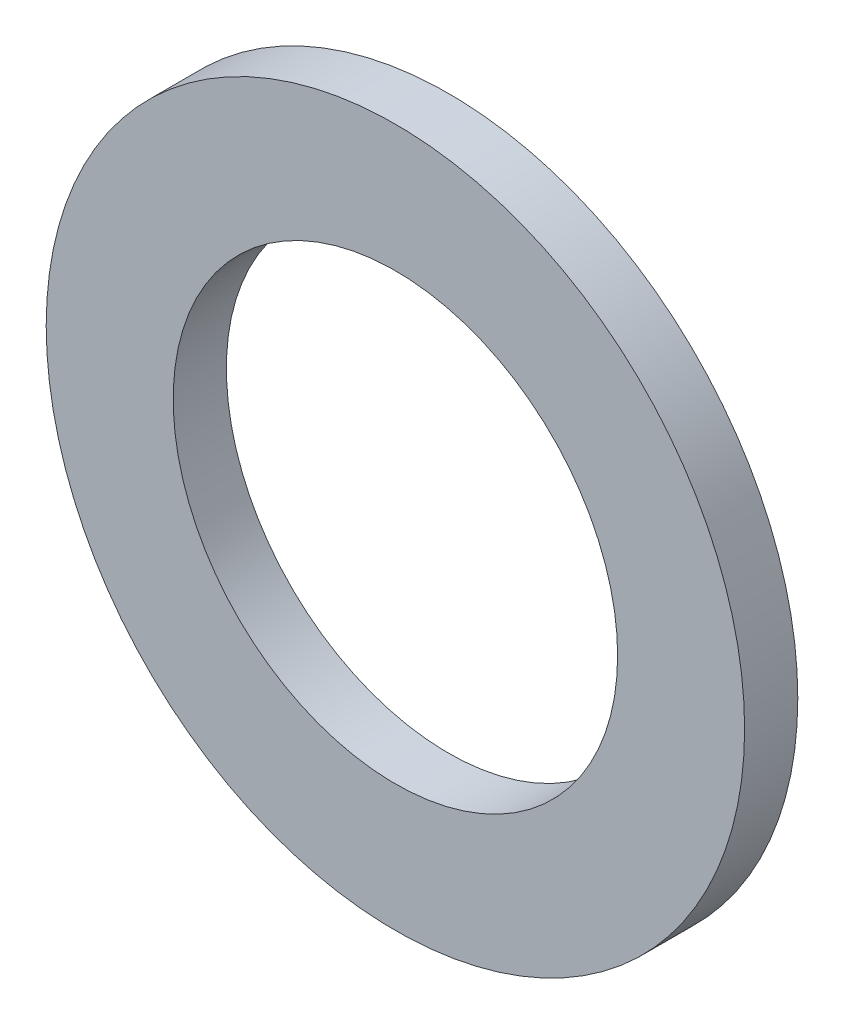
SolidWorks part; units mm, degrees
ref_plane "Front Plane" through (0, 0, 0) normal (0, 0, 1) x (1, 0, 0)
ref_plane "Top Plane" through (0, 0, 0) normal (0, 1, 0) x (1, 0, 0)
ref_plane "Right Plane" through (0, 0, 0) normal (1, 0, 0) x (0, 0, -1)
sketch "Sketch1" plane through (0, 0, 0) normal (0, 0, 1) x (1, 0, 0)
  circle A0 centre (0, 0) radius 14
  dimension "D1" = 28
extrude "Extrude-Thin1" add sketch "Sketch1" along normal blind 3.35 thin
